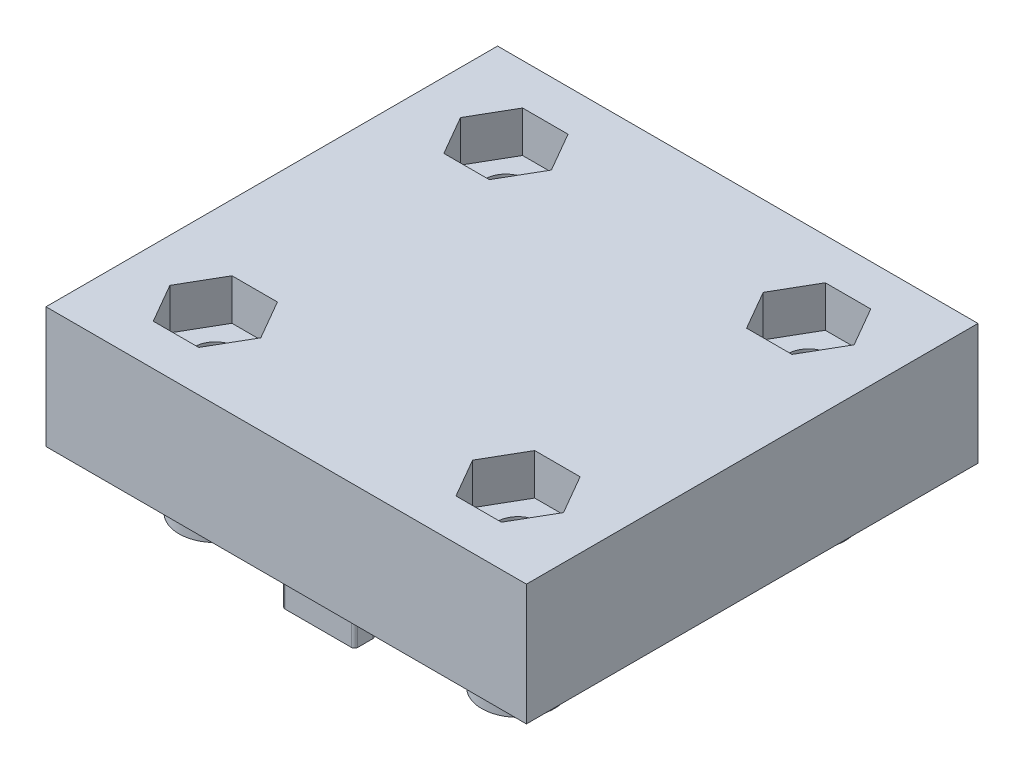
SolidWorks part; units mm, degrees
material "Nylon 101"
ref_plane "Front Plane" through (0, 0, 0) normal (0, 0, 1) x (1, 0, 0)
ref_plane "Top Plane" through (0, 0, 0) normal (0, 1, 0) x (1, 0, 0)
ref_plane "Right Plane" through (0, 0, 0) normal (1, 0, 0) x (0, 0, -1)
sketch "Sketch1" plane through (0, 0, 0) normal (0, 1, 0) x (1, 0, 0)
  line L0 (0, 18.75) -> (0, -14.7407) construction
  line L1 (-6.25, 0) -> (6.25, 0) construction
  line L7 (0, 0) -> (-16.238, -9.375) construction
  line L8 (0, 0) -> (16.238, -9.375) construction
  circle A3 centre (0, 0) radius 6.25
  point P2 (5.4127, -3.125)
  point P5 (0, 6.25)
  point P6 (-6.25, 0)
  point P7 (0, -6.25)
  point P8 (6.25, 0)
  point P11 (-5.4127, -3.125)
  dimension "D2" = 12.5
  dimension "D1" = 12.5
  dimension "D3" = 12.5
  dimension "D4" = 12.5
  dimension "D5" = 120
  dimension "D6" = 120
ref_plane "Plane4" through (0, 0, 0) normal (0, 1, 0) x (1, 0, 0)
sketch "Sketch6" plane through (0, 0, 0) normal (0, 1, 0) x (1, 0, 0)
  line L0 (-40, 33.094) -> (40, 33.094)
  line L1 (-28.6603, -16.547) -> (0, 0) construction
  line L2 (0, 0) -> (28.6603, -16.547) construction
  line L3 (28.6603, -16.547) -> (48.6603, 18.094)
  line L4 (-28.6603, -16.547) -> (-48.6603, 18.094)
  line L5 (-28.6603, -16.547) -> (-8.6603, -51.188)
  line L6 (8.6603, -51.188) -> (28.6603, -16.547)
  line L7 (0, 0) -> (-40, 23.094) construction
  line L8 (-40, 23.094) -> (40, 23.094) construction
  line L9 (40, 23.094) -> (0, 0) construction
  line L10 (0, 0) -> (0, -46.188) construction
  line L11 (0, 0) -> (-34.5631, 0) construction
  arc A0 (48.6603, 18.094) -> (40, 33.094) centre (40, 23.094) ccw
  arc A1 (-8.6603, -51.188) -> (8.6603, -51.188) centre (0, -46.188) ccw
  arc A2 (-48.6603, 18.094) -> (-40, 33.094) centre (-40, 23.094) cw
  dimension "D1" = 10
  dimension "D3" = 80
  dimension "D2" = 40
  dimension "D4" = 46.188
extrude "Boss-Extrude3" add sketch "Sketch6" along normal blind 10
ref_plane "Plane5" through (0, 10, 0) normal (0, 1, 0) x (1, 0, 0)
ref_plane "Plane10" through (0, 0, 0) normal (0, -1, 0) x (-1, 0, 0)
sketch "Sketch13" plane through (0, 0, 0) normal (0, -1, 0) x (-1, 0, 0)
  line L2 (-40, 33.094) -> (40, 33.094) construction
  line L3 (-4.5, 33.094) -> (4.5, 33.094)
  line L22 (-4.5, 33.094) -> (-4.5, 21.094)
  line L23 (-4.5, 21.094) -> (4.5, 21.094)
  line L24 (4.5, 21.094) -> (4.5, 33.094)
  point P1 (0, 33.094)
  point P5 (0, 33.094)
  dimension "D4" = 9
  dimension "D6" = 12
ref_plane "Plane14" through (0, 10, 0) normal (0, 1, 0) x (1, 0, 0)
sketch "Sketch17" plane through (0, 10, 0) normal (0, 1, 0) x (1, 0, 0)
  line L0 (-40, 33.094) -> (40, 33.094) construction
  line L1 (0, 33.094) -> (0, 23.094) construction
ref_plane "Plane15" through (0, 0, 0) normal (0, -1, 0) x (-1, 0, 0)
ref_plane "Plane16" through (0, 0, 0) normal (0, -1, 0) x (-1, 0, 0)
sketch "Sketch18" plane through (0, 0, 0) normal (0, -1, 0) x (-1, 0, 0)
  point P10 (-40, 23.094)
  point P11 (40, 23.094)
  point P12 (0, -46.188)
ref_plane "Plane17" through (0, 0, 0) normal (0, -1, 0) x (-1, 0, 0)
hole_wizard "M4 Clearance Hole1" positions "Sketch19" profile "Sketch20" hole size "M4" standard "ANSI Metric" end condition through all
sketch "Sketch19" plane through (0, 0, 0) normal (0, -1, 0) x (-1, 0, 0)
  point P0 (-40, 23.094)
  point P3 (40, 23.094)
  point P6 (0, -46.188)
sketch "Sketch20" plane through (40, 0, -23.094) normal (1, 0, 0) x (0, 0, -1)
  line L0 (0, 0) -> (0, 10)
  line L1 (0, 10) -> (2.25, 10)
  line L2 (2.25, 10) -> (2.25, 0)
  line L5 (2.25, 0) -> (0, 0)
  line L11 (0, -6.35) -> (0, 107.95) construction
  dimension "Thru Hole Dia." = 4.5
  dimension "Thru Hole Depth" = 10
sketch "Sketch21" plane through (0, 0, 0) normal (0, -1, 0) x (-1, 0, 0)
  circle A0 centre (0, 0) radius 1.118
extrude "Boss-Extrude6" add sketch "Sketch21" along normal blind 1
sketch "Sketch24" plane through (0, 0, 0) normal (1, 0, 0) x (0, 0, -1)
  line L0 (27.094, 10) -> (33.094, 2.2145)
  line L1 (33.094, 10) -> (18.094, 10) construction
  line L2 (33.094, 10) -> (33.094, 0) construction
  line L3 (33.094, 2.2145) -> (33.094, 10)
  line L4 (33.094, 10) -> (27.094, 10)
  dimension "D1" = 6
  dimension "D2" = 52.38
extrude "Cut-Extrude11" cut sketch "Sketch24" against normal mid plane 30
sketch "Sketch22" plane through (0, -1, 0) normal (0, -1, 0) x (-1, 0, 0)
  circle A0 centre (0, 0) radius 1.118
  circle A1 centre (0, 0) radius 1.118 construction
extrude "Cut-Extrude8" cut sketch "Sketch22" against normal up to surface (1 mm away) up to face at (0, 0, 1.118)
chamfer "Chamfer1" distance 1 angle 46 7 edges at (48.6603, 10, -28.094) (-27.5, 10, -33.094) (27.5, 10, -33.094) (28.6603, 10, 16.547) (-48.6603, 10, -28.094) (0, 10, 56.188) (-28.6603, 10, 16.547)
sketch "Sketch23" plane through (0, 10, 0) normal (0, 1, 0) x (1, 0, 0)
  line L0 (38.2391, 26.144) -> (36.4782, 23.094)
  line L1 (-38.2391, 20.044) -> (-36.4782, 23.094)
  line L2 (-36.4782, 23.094) -> (-38.2391, 26.144)
  line L3 (-38.2391, 26.144) -> (-41.7609, 26.144)
  line L4 (-41.7609, 26.144) -> (-43.5218, 23.094)
  line L5 (-43.5218, 23.094) -> (-41.7609, 20.044)
  line L6 (-41.7609, 20.044) -> (-38.2391, 20.044)
  line L7 (36.4782, 23.094) -> (38.2391, 20.044)
  line L8 (38.2391, 20.044) -> (41.7609, 20.044)
  line L9 (41.7609, 20.044) -> (43.5218, 23.094)
  line L10 (43.5218, 23.094) -> (41.7609, 26.144)
  line L11 (41.7609, 26.144) -> (38.2391, 26.144)
  line L12 (3.5218, -46.188) -> (1.7609, -43.138)
  line L13 (1.7609, -43.138) -> (-1.7609, -43.138)
  line L14 (-1.7609, -43.138) -> (-3.5218, -46.188)
  line L15 (-3.5218, -46.188) -> (-1.7609, -49.238)
  line L16 (-1.7609, -49.238) -> (1.7609, -49.238)
  line L17 (1.7609, -49.238) -> (3.5218, -46.188)
  circle A0 centre (-40, 23.094) radius 3.05 construction
  circle A1 centre (0, 0) radius 6.4089 construction
  circle A2 centre (0, 0) radius 6.4089 construction
  circle A3 centre (40, 23.094) radius 3.05 construction
  circle A4 centre (0, 0) radius 6.4089 construction
  circle A5 centre (0, -46.188) radius 3.05 construction
  circle A6 centre (-40, 23.094) radius 2.25 construction
  dimension "D1" = 6.1
  dimension "D2" = 3
extrude "Cut-Extrude10" cut sketch "Sketch23" against normal blind 3
sketch "Sketch25" plane through (0, 0, 0) normal (0, -1, 0) x (1, 0, 0)
  line L0 (-12.5, 15) -> (12.5, 15) construction
  line L5 (-12.5, -15) -> (12.5, 15) construction
  line L6 (-12.5, 15) -> (12.5, -15) construction
  line L7 (12.5, 15) -> (12.5, -15) construction
  line L8 (12.5, -15) -> (-12.5, -15) construction
  line L9 (-12.5, 15) -> (-12.5, -15) construction
  line L10 (-12.5, -15) -> (-12.5, -12) construction
  line L11 (0, 15) -> (0, -15) construction
  circle A0 centre (-12.5, -12) radius 1.75
  circle A1 centre (12.5, -12) radius 1.75
  point P0 (0, 0)
  dimension "D4" = 3
  dimension "D3" = 3.5
  dimension "D1" = 30
  dimension "D2" = 25
extrude "Cut-Extrude12" cut sketch "Sketch25" against normal through all both and the other way through all
mirror "Mirror1" about plane through (0, 0, 0) normal (0, 0, 1) of "Cut-Extrude12"
sketch "Sketch26" plane through (0, 10, 0) normal (0, 1, 0) x (1, 0, 0)
  line L0 (-41.7609, 20.044) -> (-38.2391, 20.044) construction
  line L1 (-16.2528, 12) -> (-14.3764, 8.75)
  line L2 (-14.3764, 8.75) -> (-10.6236, 8.75)
  line L3 (-10.6236, 8.75) -> (-8.7472, 12)
  line L4 (-8.7472, 12) -> (-10.6236, 15.25)
  line L5 (-10.6236, 15.25) -> (-14.3764, 15.25)
  line L6 (-14.3764, 15.25) -> (-16.2528, 12)
  circle A0 centre (-12.5, 12) radius 3.25 construction
  dimension "D1" = 6.5
extrude "Cut-Extrude13" cut sketch "Sketch26" against normal blind 3.4
mirror "Mirror2" about plane through (0, 0, 0) normal (1, 0, 0) of "Cut-Extrude13"
mirror "Mirror3" about plane through (0, 0, 0) normal (0, 0, 1) of "Mirror2", "Cut-Extrude13"
sketch "Sketch27" plane through (0, 0, 0) normal (0, -1, 0) x (1, 0, 0)
  circle A0 centre (-12.5, -12) radius 1.7
  circle A1 centre (-12.5, -12) radius 3
  dimension "D1" = 3.4
  dimension "D2" = 6
extrude "Boss-Extrude7" add sketch "Sketch27" along normal blind 4.4
mirror "Mirror4" about plane through (0, 0, 0) normal (0, 0, 1) of "Boss-Extrude7"
mirror "Mirror5" about plane through (0, 0, 0) normal (1, 0, 0) of "Mirror4", "Boss-Extrude7"
fillet "Fillet3" radius 2.1 4 edges at (12.5, 0, -15) (-12.5, 0, -9) (12.5, 0, 15) (-12.5, 0, 15)
sketch "Sketch28" plane through (0, -4.4, 0) normal (0, -1, 0) x (1, 0, 0)
  line L0 (10.8, -12) -> (10.05, -12) construction
  line L6 (10.05, -12) -> (10.05, -15.9887)
  line L7 (10.05, -15.9887) -> (8.2219, -15.9887)
  line L8 (8.2219, -15.9887) -> (8.2219, -5.587)
  line L9 (8.2219, -5.587) -> (10.05, -5.587)
  line L10 (10.05, -5.587) -> (10.05, -12)
  circle A0 centre (12.5, -12) radius 1.7 construction
  dimension "D1" = 0.75
  dimension "D2" = 10.4017
  dimension "D3" = 1.8281
  dimension "D4" = 6.413
extrude "Cut-Extrude14" cut sketch "Sketch28" against normal blind 2
mirror "Mirror6" about plane through (0, 0, 0) normal (1, 0, 0) of "Cut-Extrude14"
mirror "Mirror7" about plane through (0, 0, 0) normal (0, 0, 1) of "Mirror6", "Cut-Extrude14"
sketch "Sketch29" plane through (0, -4.4, 0) normal (0, -1, 0) x (1, 0, 0)
  line L0 (12.5, -10.3) -> (12.5, -9.9) construction
  line L1 (12.5, -9.9) -> (6.9536, -9.9)
  line L2 (6.9536, -9.9) -> (6.9536, -8.0978)
  line L3 (6.9536, -8.0978) -> (18.6708, -8.0978)
  line L4 (12.5, -9.9) -> (18.6708, -9.9)
  line L5 (18.6708, -9.9) -> (18.6708, -8.0978)
  circle A0 centre (12.5, -12) radius 1.7 construction
  dimension "D1" = 0.4
  dimension "D2" = 1.8022
  dimension "D3" = 11.7172
  dimension "D4" = 5.5464
extrude "Cut-Extrude15" cut sketch "Sketch29" against normal blind 4
fillet "Fillet6" radius 0.25 2 edges at (10.05, -3.4, -13.7313) (9.5, -2.4, -12)
fillet "Fillet7" radius 0.25 9 edges at (-10.05, -3.4, 13.7313) (-10.05, -3.4, 10.2687) (-10.05, -3.4, -13.7313) (-10.05, -3.4, -10.2687) (10.05, -3.4, 13.7313) (10.05, -3.4, 10.2687) (9.5, -2.4, 12) (-9.5, -2.4, 12) (-9.5, -2.4, -12)
sketch "Sketch30" plane through (0, 0, 0) normal (0, -1, 0) x (1, 0, 0)
  line L0 (0, -15) -> (3, -15) construction
  line L1 (-12.5, -15) -> (12.5, -15) construction
  line L2 (-12.5, -15) -> (-12.5, 15) construction
  line L3 (-12.5, 15) -> (12.5, 15) construction
  line L4 (12.5, -15) -> (12.5, 15) construction
  line L5 (-12.5, -15) -> (12.5, 15) construction
  line L6 (-12.5, 15) -> (12.5, -15) construction
  line L11 (3, -15) -> (3, -14.25)
  line L12 (3, -14.25) -> (-3, -14.25)
  line L13 (-3, -14.25) -> (-3, -15)
  line L14 (-3, -15) -> (-3, -16)
  line L15 (-3, -16) -> (3, -16)
  line L16 (3, -16) -> (3, -15)
  point P0 (0, 0)
  point P6 (0, -15)
  dimension "D1" = 25
  dimension "D2" = 30
  dimension "D3" = 3
  dimension "D4" = 0.75
  dimension "D5" = 6
  dimension "D6" = 1
extrude "Boss-Extrude8" add sketch "Sketch30" along normal blind 4.4
fillet "Fillet8" radius 0.25 4 edges at (3, -2.2, -14.25) (3, -2.2, -16) (-3, -2.2, -16) (-3, -2.2, -14.25)
mirror "Mirror8" about plane through (0, 0, 0) normal (0, 0, 1) of "Boss-Extrude8"
fillet "Fillet9" radius 1 8 edges at (-2.9268, 0, -14.3232) (0, 0, -14.25) (2.9268, 0, -14.3232) (3, 0, -15.125) (2.9268, 0, -15.9268) (0, 0, -16) (-2.9268, 0, -15.9268) (-3, 0, -15.125)
fillet "Fillet10" radius 0.25 4 edges at (3, -2.2, 14.25) (3, -2.2, 16) (-3, -2.2, 16) (-3, -2.2, 14.25)
fillet "Fillet11" radius 1 8 edges at (-2.9268, 0, 15.9268) (-3, 0, 15.125) (-2.9268, 0, 14.3232) (0, 0, 14.25) (2.9268, 0, 14.3232) (3, 0, 15.125) (2.9268, 0, 15.9268) (0, 0, 16)
ref_plane "Plane18" through (0, -20, 0) normal (0, -1, 0) x (-1, 0, 0)
sketch "Sketch32" plane through (0, -20, 0) normal (0, -1, 0) x (-1, 0, 0)
  line L1 (19.8381, 18.6461) -> (-19.8381, 18.6461)
  line L2 (19.8381, 18.6461) -> (19.8381, -18.6461)
  line L3 (19.8381, -18.6461) -> (-19.8381, -18.6461)
  line L4 (-19.8381, 18.6461) -> (-19.8381, -18.6461)
  line L5 (19.8381, 18.6461) -> (-19.8381, -18.6461) construction
  line L6 (19.8381, -18.6461) -> (-19.8381, 18.6461) construction
  line L7 (-74.1508, -65.4098) -> (74.1508, -65.4098)
  line L8 (-74.1508, -65.4098) -> (-74.1508, 65.4098)
  line L9 (-74.1508, 65.4098) -> (74.1508, 65.4098)
  line L10 (74.1508, -65.4098) -> (74.1508, 65.4098)
  line L11 (-74.1508, -65.4098) -> (74.1508, 65.4098) construction
  line L12 (-74.1508, 65.4098) -> (74.1508, -65.4098) construction
  point P0 (0, 0)
  point P6 (0, 0)
extrude "Cut-Extrude16" cut sketch "Sketch32" against normal blind 40
